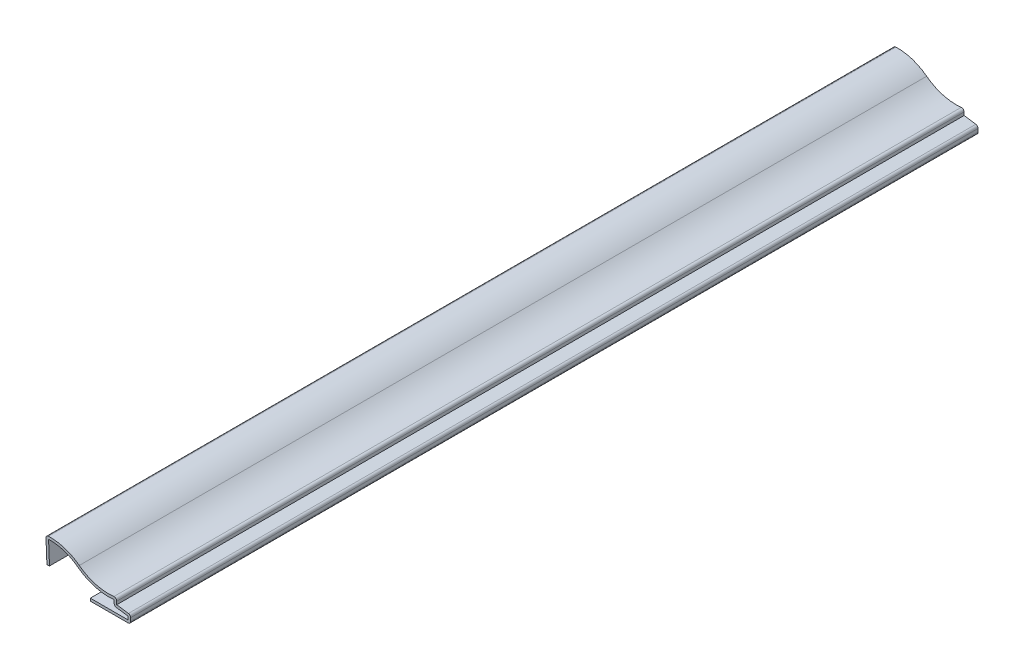
SolidWorks part; units mm, degrees
ref_plane "Front Plane" through (0, 0, 0) normal (0, 0, 1) x (1, 0, 0)
ref_plane "Top Plane" through (0, 0, 0) normal (0, 1, 0) x (1, 0, 0)
ref_plane "Right Plane" through (0, 0, 0) normal (1, 0, 0) x (0, 0, -1)
sketch "Sketch1" plane through (0, 0, 0) normal (0, 0, 1) x (1, 0, 0)
  line L0 (0, 0) -> (-0.3969, 9.9219)
  line L1 (27.473, 2.4475) -> (27.473, 0.0663)
  line L2 (27.473, 0.0663) -> (32.9406, -0.7275)
  line L3 (32.9406, -0.7275) -> (32.9406, -3.9025)
  line L4 (32.9406, -3.9025) -> (17.0656, -3.9025)
  arc A0 (-0.3969, 9.9219) -> (12.7443, 6.0846) centre (1.1906, -9.0619) cw
  arc A1 (12.7443, 6.0846) -> (27.473, 2.4475) centre (24.298, 21.2311) ccw
  point P7 (0, 0)
  point P12 (3.8872, 1.8419)
  point P13 (26.5946, 8.8099)
  point P14 (-0.3969, 12.7448)
  point P15 (26.2257, 3.4146)
  point P16 (16.4342, 8.2998)
  point P17 (15.7538, -0.6028)
  point P18 (12.2988, 6.0526)
  dimension "D3" = 19.05
  dimension "D4" = 19.05
  dimension "D11" = 13.8906
  dimension "D1" = 0.3969
  dimension "D2" = 33.3375
  dimension "D5" = 2.3813
  dimension "D6" = 0.7937
  dimension "D7" = 15.875
  dimension "D8" = 9.9219
  dimension "D9" = 3.175
  dimension "D10" = 3.175
  dimension "D12" = 1.5875
extrude "Extrude-Thin1" add sketch "Sketch1" against normal blind 333.375 thin
fillet "Fillet1" radius 1.016 5 edges at (26.457, -0.8129, -166.6875) (32.9406, -3.9025, -166.6875) (32.9406, -0.7275, -166.6875) (27.473, 2.4475, -166.6875) (-0.3969, 9.9219, -166.6875)
